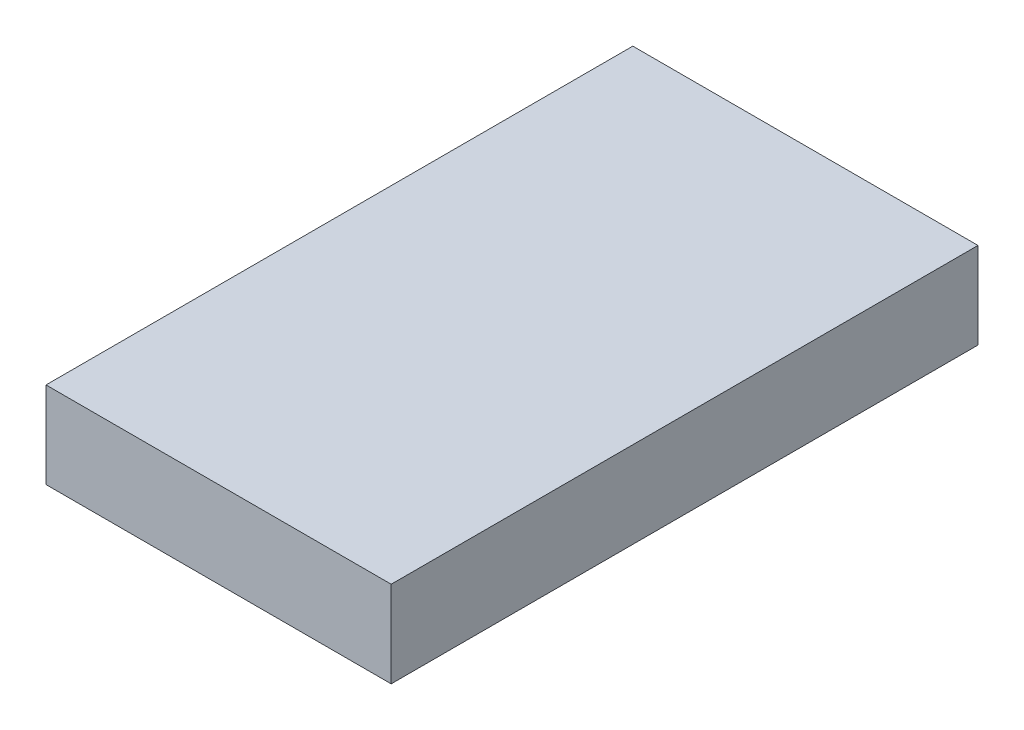
SolidWorks part; units mm, degrees
ref_plane "Front" through (0, 0, 0) normal (0, 0, 1) x (1, 0, 0)
ref_plane "Top" through (0, 0, 0) normal (0, 1, 0) x (1, 0, 0)
ref_plane "Right" through (0, 0, 0) normal (1, 0, 0) x (0, 0, -1)
sketch "Sketch1" plane through (0, 0, 0) normal (0, 1, 0) x (1, 0, 0)
  line L1 (-60, -102) -> (60, -102)
  line L2 (-60, -102) -> (-60, 102)
  line L3 (-60, 102) -> (60, 102)
  line L4 (60, -102) -> (60, 102)
  line L5 (-60, -102) -> (60, 102) construction
  line L6 (-60, 102) -> (60, -102) construction
  point P0 (0, 0)
  dimension "D1" = 204
  dimension "D2" = 120
extrude "Boss-Extrude1" add sketch "Sketch1" along normal blind 30
